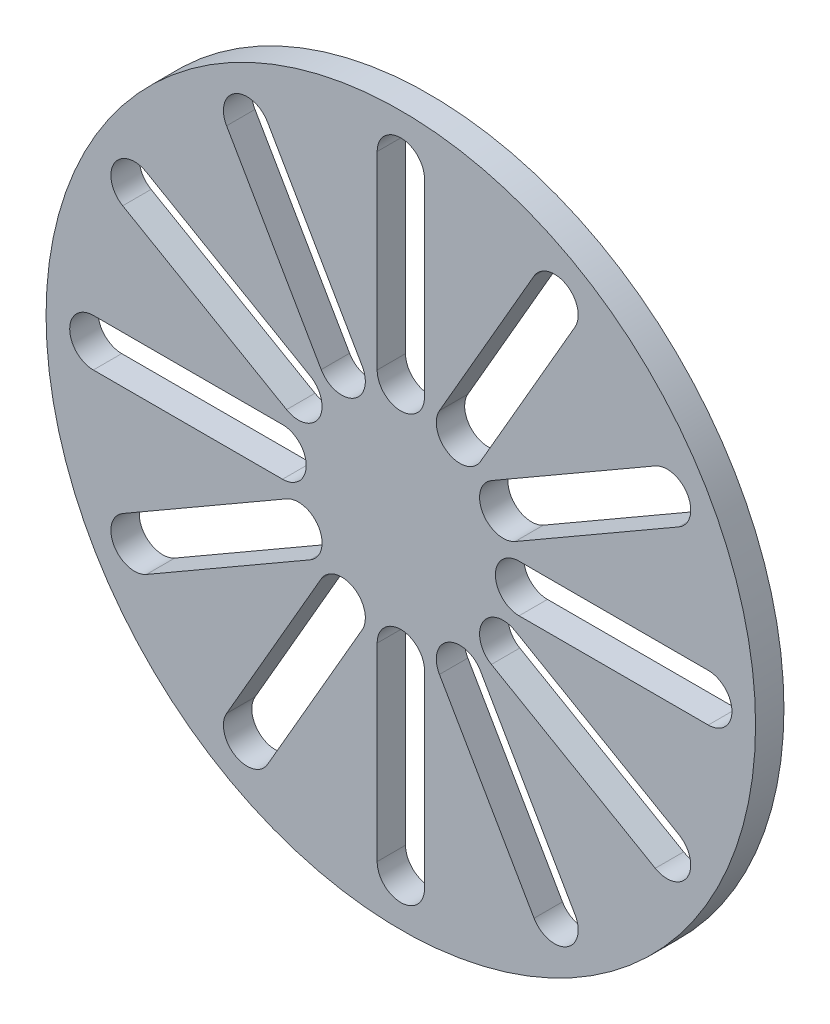
SolidWorks part; units mm, degrees
ref_plane "Front Plane" through (0, 0, 0) normal (0, 0, 1) x (1, 0, 0)
ref_plane "Top Plane" through (0, 0, 0) normal (0, 1, 0) x (1, 0, 0)
ref_plane "Right Plane" through (0, 0, 0) normal (1, 0, 0) x (0, 0, -1)
sketch "Sketch1" plane through (0, 0, 0) normal (0, 0, 1) x (1, 0, 0)
  line L0 (-6.35, 82.55) -> (-6.35, 31.75)
  line L1 (6.35, 82.55) -> (6.35, 31.75)
  line L2 (0, 0) -> (0, 111.2058) construction
  line L3 (6.35, 57.15) -> (-6.35, 57.15) construction
  line L4 (46.7743, 68.3154) -> (21.3743, 24.3213)
  line L5 (35.7757, 74.6654) -> (10.3757, 30.6713)
  line L6 (74.6654, 35.7757) -> (30.6713, 10.3757)
  line L7 (68.3154, 46.7743) -> (24.3213, 21.3743)
  line L8 (82.55, -6.35) -> (31.75, -6.35)
  line L9 (82.55, 6.35) -> (31.75, 6.35)
  line L10 (68.3154, -46.7743) -> (24.3213, -21.3743)
  line L11 (74.6654, -35.7757) -> (30.6713, -10.3757)
  line L12 (35.7757, -74.6654) -> (10.3757, -30.6713)
  line L13 (46.7743, -68.3154) -> (21.3743, -24.3213)
  line L14 (-6.35, -82.55) -> (-6.35, -31.75)
  line L15 (6.35, -82.55) -> (6.35, -31.75)
  line L16 (-46.7743, -68.3154) -> (-21.3743, -24.3213)
  line L17 (-35.7757, -74.6654) -> (-10.3757, -30.6713)
  line L18 (-74.6654, -35.7757) -> (-30.6713, -10.3757)
  line L19 (-68.3154, -46.7743) -> (-24.3213, -21.3743)
  line L20 (-82.55, 6.35) -> (-31.75, 6.35)
  line L21 (-82.55, -6.35) -> (-31.75, -6.35)
  line L22 (-68.3154, 46.7743) -> (-24.3213, 21.3743)
  line L23 (-74.6654, 35.7757) -> (-30.6713, 10.3757)
  line L24 (-35.7757, 74.6654) -> (-10.3757, 30.6713)
  line L25 (-46.7743, 68.3154) -> (-21.3743, 24.3213)
  circle A0 centre (0, 0) radius 95.25
  arc A1 (-6.35, 31.75) -> (6.35, 31.75) centre (0, 31.75) ccw
  arc A2 (6.35, 82.55) -> (-6.35, 82.55) centre (0, 82.55) ccw
  circle A3 centre (0, 0) radius 57.15 construction
  circle A4 centre (0, 0) radius 57.15
  arc A5 (10.3757, 30.6713) -> (21.3743, 24.3213) centre (15.875, 27.4963) ccw
  arc A6 (46.7743, 68.3154) -> (35.7757, 74.6654) centre (41.275, 71.4904) ccw
  circle A7 centre (0, 0) radius 57.15
  arc A8 (24.3213, 21.3743) -> (30.6713, 10.3757) centre (27.4963, 15.875) ccw
  arc A9 (74.6654, 35.7757) -> (68.3154, 46.7743) centre (71.4904, 41.275) ccw
  circle A10 centre (0, 0) radius 57.15
  arc A11 (31.75, 6.35) -> (31.75, -6.35) centre (31.75, 0) ccw
  arc A12 (82.55, -6.35) -> (82.55, 6.35) centre (82.55, 0) ccw
  circle A13 centre (0, 0) radius 57.15
  arc A14 (30.6713, -10.3757) -> (24.3213, -21.3743) centre (27.4963, -15.875) ccw
  arc A15 (68.3154, -46.7743) -> (74.6654, -35.7757) centre (71.4904, -41.275) ccw
  circle A16 centre (0, 0) radius 57.15
  arc A17 (21.3743, -24.3213) -> (10.3757, -30.6713) centre (15.875, -27.4963) ccw
  arc A18 (35.7757, -74.6654) -> (46.7743, -68.3154) centre (41.275, -71.4904) ccw
  circle A19 centre (0, 0) radius 57.15
  arc A20 (6.35, -31.75) -> (-6.35, -31.75) centre (0, -31.75) ccw
  arc A21 (-6.35, -82.55) -> (6.35, -82.55) centre (0, -82.55) ccw
  circle A22 centre (0, 0) radius 57.15
  arc A23 (-10.3757, -30.6713) -> (-21.3743, -24.3213) centre (-15.875, -27.4963) ccw
  arc A24 (-46.7743, -68.3154) -> (-35.7757, -74.6654) centre (-41.275, -71.4904) ccw
  circle A25 centre (0, 0) radius 57.15
  arc A26 (-24.3213, -21.3743) -> (-30.6713, -10.3757) centre (-27.4963, -15.875) ccw
  arc A27 (-74.6654, -35.7757) -> (-68.3154, -46.7743) centre (-71.4904, -41.275) ccw
  circle A28 centre (0, 0) radius 57.15
  arc A29 (-31.75, -6.35) -> (-31.75, 6.35) centre (-31.75, 0) ccw
  arc A30 (-82.55, 6.35) -> (-82.55, -6.35) centre (-82.55, 0) ccw
  circle A31 centre (0, 0) radius 57.15
  arc A32 (-30.6713, 10.3757) -> (-24.3213, 21.3743) centre (-27.4963, 15.875) ccw
  arc A33 (-68.3154, 46.7743) -> (-74.6654, 35.7757) centre (-71.4904, 41.275) ccw
  circle A34 centre (0, 0) radius 57.15
  arc A35 (-21.3743, 24.3213) -> (-10.3757, 30.6713) centre (-15.875, 27.4963) ccw
  arc A36 (-35.7757, 74.6654) -> (-46.7743, 68.3154) centre (-41.275, 71.4904) ccw
  point P3 (0, 31.75)
  point P4 (0, 82.55)
  point P96 (0, 0)
  dimension "D1" = 190.5
  dimension "D4" = 12.7
  dimension "D2" = 31.75
  dimension "D3" = 50.8
  dimension "D5" = 12
extrude "Boss-Extrude1" add sketch "Sketch1" along normal blind 7.62 contours A0 A36 L24 A3 L0 A2 L1 L5 A6 L4 L7 A9 L6 L9 A12 L8 L11 A15 L10 L13 A18 L12 L15 A21 L14 L17 A24 L16 L19 A27 L18 L21 A30 L20 L23 A33 L22 L25 | A35 L25 A3 L22 A32 L23 L20 A29 L21 L18 A26 L19 L16 A23 L17 L14 A20 L15 L12 A17 L13 L10 A14 L11 L8 A11 L9 L6 A8 L7 L4 A5 L5 L1 A1 L0 L24
